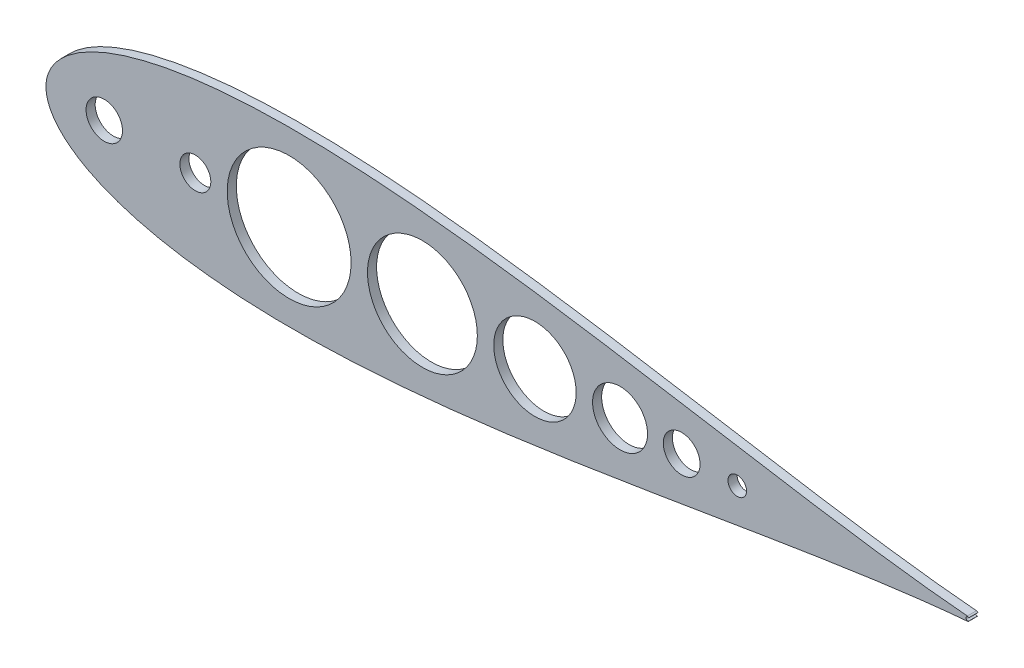
SolidWorks part; units mm, degrees
material "Balsa"
ref_plane "Front Plane" through (0, 0, 0) normal (0, 0, 1) x (1, 0, 0)
ref_plane "Top Plane" through (0, 0, 0) normal (0, 1, 0) x (1, 0, 0)
ref_plane "Right Plane" through (0, 0, 0) normal (1, 0, 0) x (0, 0, -1)
curve "Curve4"
  spline degree 3 poles (100, 0, 0) (99.8498, 0.0023, 0) (99.4759, 0.008, 0) (99.1023, 0.0238, 0) (98.8789, 0.0332, 0) knots 0 0 0 0 0.401829 1 1 1 1
curve "Curve5"
  spline degree 3 poles (99.3714, -0.0082, 0) (100.2526, 0, 0) (99.3714, 0.0082, 0) (98.8504, 0.035, 0) (97.904, 0.0811, 0) (96.8285, 0.1543, 0) (95.5159, 0.2583, 0) (94.013, 0.3972, 0) (92.313, 0.574, 0) (90.4281, 0.791, 0) (88.3655, 1.0495, 0) (86.1348, 1.3497, 0) (83.7456, 1.691, 0) (81.2082, 2.0715, 0) (78.5335, 2.4886, 0) (75.7326, 2.9386, 0) (72.8172, 3.4168, 0) (69.799, 3.9177, 0) (66.6904, 4.435, 0) (63.5039, 4.9616, 0) (60.2521, 5.4899, 0) (56.948, 6.0119, 0) (53.6049, 6.519, 0) (50.2363, 7.0024, 0) (46.8558, 7.4534, 0) (43.4774, 7.8632, 0) (40.1152, 8.2232, 0) (36.7837, 8.5249, 0) (33.4975, 8.7606, 0) (30.2716, 8.923, 0) (27.1211, 9.0055, 0) (24.0614, 9.0025, 0) (21.108, 8.909, 0) (18.277, 8.7213, 0) (15.5843, 8.4369, 0) (13.0466, 8.0543, 0) (10.6806, 7.5735, 0) (8.5039, 6.996, 0) (6.5349, 6.3253, 0) (4.7933, 5.5673, 0) (3.3001, 4.7321, 0) (2.0777, 3.8366, 0) (1.1467, 2.91, 0) (0.5165, 2.0014, 0) (0.165, 1.1816, 0) (0.0231, 0.524, 0) (-0.0093, 0, 0) (0.0231, -0.524, 0) (0.165, -1.1816, 0) (0.5165, -2.0014, 0) (1.1467, -2.91, 0) (2.0777, -3.8366, 0) (3.3001, -4.7321, 0) (4.7933, -5.5673, 0) (6.5349, -6.3253, 0) (8.5039, -6.996, 0) (10.6806, -7.5735, 0) (13.0466, -8.0543, 0) (15.5843, -8.4369, 0) (18.277, -8.7213, 0) (21.108, -8.909, 0) (24.0614, -9.0025, 0) (27.1211, -9.0055, 0) (30.2716, -8.923, 0) (33.4975, -8.7606, 0) (36.7837, -8.5249, 0) (40.1152, -8.2232, 0) (43.4774, -7.8632, 0) (46.8558, -7.4534, 0) (50.2363, -7.0024, 0) (53.6049, -6.519, 0) (56.948, -6.0119, 0) (60.2521, -5.4899, 0) (63.5039, -4.9616, 0) (66.6904, -4.435, 0) (69.799, -3.9177, 0) (72.8172, -3.4168, 0) (75.7326, -2.9386, 0) (78.5335, -2.4886, 0) (81.2082, -2.0715, 0) (83.7456, -1.691, 0) (86.1348, -1.3497, 0) (88.3655, -1.0495, 0) (90.4281, -0.791, 0) (92.313, -0.574, 0) (94.013, -0.3972, 0) (95.5159, -0.2583, 0) (96.8285, -0.1543, 0) (97.904, -0.0811, 0) (98.8504, -0.035, 0) (99.3714, -0.0082, 0) (100.2526, 0, 0) (99.3714, 0.0082, 0) knots -0.009667 -0.005395 -0.002168 0 0.002168 0.005395 0.009667 0.014967 0.021271 0.028553 0.036781 0.04592 0.055932 0.066773 0.078397 0.090755 0.103793 0.117456 0.131686 0.146422 0.1616 0.177156 0.193024 0.209135 0.225421 0.241812 0.258238 0.274629 0.290914 0.307025 0.322893 0.338448 0.353626 0.368361 0.38259 0.396253 0.40929 0.421647 0.43327 0.444109 0.454119 0.463255 0.471479 0.478755 0.485052 0.490344 0.49461 0.497833 0.5 0.502167 0.50539 0.509656 0.514948 0.521245 0.528521 0.536745 0.545881 0.555891 0.56673 0.578353 0.59071 0.603747 0.61741 0.631639 0.646374 0.661552 0.677107 0.692975 0.709086 0.725371 0.741762 0.758188 0.774579 0.790865 0.806976 0.822844 0.8384 0.853578 0.868314 0.882544 0.896207 0.909245 0.921603 0.933227 0.944068 0.95408 0.963219 0.971447 0.978729 0.985033 0.990333 0.994605 0.997832 1 1.002168 1.005395 1.009667 periodic
sketch "Sketch2" plane through (0, 0, 0) normal (0, 0, 1) x (1, 0, 0)
  line L0 (100, 0) -> (0, 0) construction
  line L2 (93.345, 0) -> (114.935, 0) construction
  line L4 (643.5991, 0) -> (643.5991, -1.016)
  line L9 (0, 0) -> (643.9668, 0)
  line L13 (460.661, 0) -> (473.361, 0)
  circle A0 centre (104.14, 0) radius 10.795 construction
  arc A2 (641.5671, 0) -> (644.1071, 0) centre (642.8371, 0) ccw
  circle A4 centre (104.14, 0) radius 10.795
  circle A9 centre (40.64, 0) radius 12.7
  circle A14 centre (642.3793, 0) radius 1.5875 construction
  arc A15 (642.5108, -1.582) -> (642.5108, 1.582) centre (642.3793, 0) ccw
  spline S2 degree 3 poles (666.3448, -0.0547) (672.2538, 0) (666.3448, 0.0547) (662.8509, 0.2344) (656.505, 0.5436) (649.293, 1.0348) (640.4916, 1.7319) (630.4138, 2.6634) (619.0141, 3.8493) (606.375, 5.3044) (592.5439, 7.0376) (577.5855, 9.0506) (561.5643, 11.3389) (544.5497, 13.8907) (526.6141, 16.6877) (507.8326, 19.7051) (488.2827, 22.9117) (468.0444, 26.2704) (447.1994, 29.739) (425.8316, 33.2703) (404.0263, 36.8132) (381.8707, 40.3133) (359.4533, 43.7135) (336.8645, 46.9554) (314.1962, 49.9798) (291.5418, 52.7277) (268.9963, 55.1412) (246.6566, 57.1646) (224.6209, 58.7452) (202.9892, 59.8341) (181.8631, 60.3875) (161.3458, 60.367) (141.542, 59.7399) (122.5581, 58.4818) (104.5023, 56.5743) (87.485, 54.0089) (71.6197, 50.7848) (57.0237, 46.9125) (43.8205, 42.415) (32.1416, 37.3322) (22.1291, 31.7315) (13.9324, 25.7264) (7.6896, 19.5132) (3.4631, 13.4204) (1.1063, 7.9234) (0.1546, 3.5138) (-0.0622, 0) (0.1546, -3.5138) (1.1063, -7.9234) (3.4631, -13.4204) (7.6896, -19.5132) (13.9324, -25.7264) (22.1291, -31.7315) (32.1416, -37.3322) (43.8205, -42.415) (57.0237, -46.9125) (71.6197, -50.7848) (87.485, -54.0089) (104.5023, -56.5743) (122.5581, -58.4818) (141.542, -59.7399) (161.3458, -60.367) (181.8631, -60.3875) (202.9892, -59.8341) (224.6209, -58.7452) (246.6566, -57.1646) (268.9963, -55.1412) (291.5418, -52.7277) (314.1962, -49.9798) (336.8645, -46.9554) (359.4533, -43.7135) (381.8707, -40.3133) (404.0263, -36.8132) (425.8316, -33.2703) (447.1994, -29.739) (468.0444, -26.2704) (488.2827, -22.9117) (507.8326, -19.7051) (526.6141, -16.6877) (544.5497, -13.8907) (561.5643, -11.3389) (577.5855, -9.0506) (592.5439, -7.0376) (606.375, -5.3044) (619.0141, -3.8493) (630.4138, -2.6634) (640.4916, -1.7319) (649.293, -1.0348) (656.505, -0.5436) (662.8509, -0.2344) (666.3448, -0.0547) (672.2538, 0) (666.3448, 0.0547) knots -0.009667 -0.005395 -0.002168 0 0.002168 0.005395 0.009667 0.014967 0.021271 0.028553 0.036781 0.04592 0.055932 0.066773 0.078397 0.090755 0.103793 0.117456 0.131686 0.146422 0.1616 0.177156 0.193024 0.209135 0.225421 0.241812 0.258238 0.274629 0.290914 0.307025 0.322893 0.338448 0.353626 0.368361 0.38259 0.396253 0.40929 0.421647 0.43327 0.444109 0.454119 0.463255 0.471479 0.478755 0.485052 0.490344 0.49461 0.497833 0.5 0.502167 0.50539 0.509656 0.514948 0.521245 0.528521 0.536745 0.545881 0.555891 0.56673 0.578353 0.59071 0.603747 0.61741 0.631639 0.646374 0.661552 0.677107 0.692975 0.709086 0.725371 0.741762 0.758188 0.774579 0.790865 0.806976 0.822844 0.8384 0.853578 0.868314 0.882544 0.896207 0.909245 0.921603 0.933227 0.944068 0.95408 0.963219 0.971447 0.978729 0.985033 0.990333 0.994605 0.997832 1 1.002168 1.005395 1.009667 only from (670.56, 0) to (670.56, 0)
  point P2 (167.64, 0)
  dimension "D2" = 21.59
  dimension "D8" = 25.4
  dimension "D10" = 3.175
  dimension "D1" = 167.64
  dimension "D6" = 63.5
  dimension "D9" = 63.5
  dimension "D3" = 1.016
  dimension "D4" = 1.27
extrude "Boss-Extrude1" add sketch "Sketch2" along normal blind 6.35
sketch "Sketch3" plane through (0, 0, 6.35) normal (0, 0, 1) x (1, 0, 0)
  line L0 (84.14, -12.7) -> (62.637, -12.7) construction
  line L1 (430.4749, -1041.2705) -> (430.4749, 48958.7295) construction
  line L2 (114.935, 0) -> (641.5671, 0) construction
  line L3 (27.94, 0) -> (0, 0)
  line L4 (641.5671, 0) -> (114.935, 0)
  line L5 (93.345, 0) -> (53.34, 0)
  line L6 (27.94, 0) -> (0, 0)
  line L7 (212.768, -1000) -> (212.768, 49000) construction
  line L8 (93.345, 0) -> (53.34, 0)
  line L9 (224.198, -1000) -> (224.198, 49000) construction
  line L10 (300.8092, -1000) -> (300.8092, 49000) construction
  line L11 (312.2392, -1000) -> (312.2392, 49000) construction
  line L12 (369.7207, -1000) -> (369.7207, 49000) construction
  line L13 (93.345, -17.145) -> (65.0689, -17.145) construction
  line L14 (419.5047, -1000) -> (419.5047, 49000) construction
  line L15 (126.365, -1000) -> (126.365, 49000) construction
  line L16 (381.1507, -1000) -> (381.1507, 49000) construction
  line L17 (52.7726, -27.2676) -> (52.7726, -27.2676) construction
  arc A0 (36.4352, -25.0495) -> (62.637, -12.7) centre (40.64, 0) ccw construction
  circle A2 centre (169.5665, 0) radius 43.2015
  arc A3 (642.5108, -1.582) -> (643.5991, -1.016) centre (642.3793, 0) ccw
  arc A4 (93.345, 0) -> (114.935, 0) centre (104.14, 0) ccw
  arc A5 (27.94, 0) -> (53.34, 0) centre (40.64, 0) ccw
  arc A6 (642.5108, -1.582) -> (643.5991, -1.016) centre (642.3793, 0) ccw
  circle A7 centre (262.5036, 0) radius 38.3056
  arc A8 (27.94, 0) -> (53.34, 0) centre (40.64, 0) ccw
  circle A9 centre (340.9799, 0) radius 28.7408
  circle A10 centre (400.3277, 0) radius 19.177
  circle A11 centre (443.3019, 0) radius 12.827
  circle A12 centre (482.0825, 0) radius 6.477
  arc A13 (52.7726, -27.2676) -> (65.0689, -17.145) centre (40.64, 0) ccw construction
  arc A14 (638.2053, 15.2585) -> (638.2053, 15.2585) centre (638.2053, 15.2585) ccw construction
  arc A18 (641.5671, 0) -> (643.5991, -1.016) centre (642.8371, 0) ccw
  arc A19 (641.5671, 0) -> (643.5991, -1.016) centre (642.8371, 0) ccw
  spline S1 degree 3 poles (1488.1541, -2580.0534) (314.1987, 184.2642) (-15.4092, 68.5977) (1.1063, -7.9234) (3.4631, -13.4204) (7.6896, -19.5132) (13.9324, -25.7264) (22.1291, -31.7315) (32.1416, -37.3322) (43.8205, -42.415) (57.0237, -46.9125) (71.6197, -50.7848) (87.485, -54.0089) (104.5023, -56.5743) (122.5581, -58.4818) (141.542, -59.7399) (161.3458, -60.367) (181.8631, -60.3875) (202.9892, -59.8341) (224.6209, -58.7452) (246.6566, -57.1646) (268.9963, -55.1412) (291.5418, -52.7277) (314.1962, -49.9798) (336.8645, -46.9554) (359.4533, -43.7135) (381.8707, -40.3133) (404.0263, -36.8132) (425.8316, -33.2703) (447.1994, -29.739) (468.0444, -26.2704) (488.2827, -22.9117) (507.8326, -19.7051) (526.6141, -16.6877) (544.5497, -13.8907) (561.5643, -11.3389) (577.5855, -9.0506) (592.5439, -7.0376) (606.375, -5.3044) (619.0141, -3.8493) (630.4138, -2.6634) (754.7119, 8.8252) (895.5191, -9.0089) (-2343.84, -283.812) knots 0.342093 0.342093 0.342093 0.342093 0.502167 0.50539 0.509656 0.514948 0.521245 0.528521 0.536745 0.545881 0.555891 0.56673 0.578353 0.59071 0.603747 0.61741 0.631639 0.646374 0.661552 0.677107 0.692975 0.709086 0.725371 0.741762 0.758188 0.774579 0.790865 0.806976 0.822844 0.8384 0.853578 0.868314 0.882544 0.896207 0.909245 0.921603 0.933227 0.944068 0.95408 0.963219 0.971447 0.978729 1.23227 1.23227 1.23227 1.23227 only from (0, 0) to (642.5108, -1.582)
  spline S2 degree 3 poles (0, 0) (0, -1.0075) (0.1546, -3.5138) (1.1063, -7.9234) (3.4631, -13.4204) (7.6896, -19.5132) (13.9324, -25.7264) (22.1291, -31.7315) (32.1416, -37.3322) (43.8205, -42.415) (57.0237, -46.9125) (71.6197, -50.7848) (87.485, -54.0089) (104.5023, -56.5743) (122.5581, -58.4818) (141.542, -59.7399) (161.3458, -60.367) (181.8631, -60.3875) (202.9892, -59.8341) (224.6209, -58.7452) (246.6566, -57.1646) (268.9963, -55.1412) (291.5418, -52.7277) (314.1962, -49.9798) (336.8645, -46.9554) (359.4533, -43.7135) (381.8707, -40.3133) (404.0263, -36.8132) (425.8316, -33.2703) (447.1994, -29.739) (468.0444, -26.2704) (488.2827, -22.9117) (507.8326, -19.7051) (526.6141, -16.6877) (544.5497, -13.8907) (561.5643, -11.3389) (577.5855, -9.0506) (592.5439, -7.0376) (606.375, -5.3044) (619.0141, -3.8493) (630.4138, -2.6634) (638.0937, -1.9535) (641.9934, -1.6251) (642.5108, -1.582) knots 0.5 0.5 0.5 0.5 0.502167 0.50539 0.509656 0.514948 0.521245 0.528521 0.536745 0.545881 0.555891 0.56673 0.578353 0.59071 0.603747 0.61741 0.631639 0.646374 0.661552 0.677107 0.692975 0.709086 0.725371 0.741762 0.758188 0.774579 0.790865 0.806976 0.822844 0.8384 0.853578 0.868314 0.882544 0.896207 0.909245 0.921603 0.933227 0.944068 0.95408 0.963219 0.971447 0.978729 0.979843 0.979843 0.979843 0.979843
  spline S4 degree 1 poles (52.7726, -27.2676) (638.2053, 15.2585) knots 0 0 1 1 construction
  spline S5 degree 3 poles (52.7726, -27.2676) (54.098, -27.7509) (56.7529, -28.6784) (62.1794, -30.4243) (69.1006, -32.3953) (77.5892, -34.4571) (89.0862, -36.8389) (103.7331, -39.1926) (125.3657, -41.6037) (144.2709, -42.7116) (163.2853, -43.1964) (177.6693, -43.2555) (201.2447, -42.8023) (227.4371, -41.4675) (254.4928, -39.2877) (277.8401, -36.9937) (301.0423, -34.3583) (330.3789, -30.5811) (368.329, -25.1309) (404.83, -19.3409) (435.2358, -14.3425) (451.6826, -11.6119) (464.2574, -9.5208) (476.8398, -7.4307) (497.3171, -4.0443) (526.9629, 0.7645) (562.929, 6.2684) (594.1055, 10.5252) (616.0859, 13.0867) (628.694, 14.3901) (635.0364, 14.9826) (638.2053, 15.2585) knots 0.548481 0.548481 0.548481 0.548481 0.551835 0.555189 0.561898 0.568606 0.575315 0.588731 0.602148 0.62409 0.630798 0.644215 0.655815 0.682649 0.701659 0.715076 0.733763 0.752449 0.779283 0.816817 0.832298 0.845715 0.852722 0.859728 0.873145 0.897318 0.924152 0.950985 0.964402 0.971111 0.977819 0.977819 0.977819 0.977819 construction
  line M19 (641.5671, 0) -> (114.935, 0)
  dimension "D3" = 11.43
  dimension "D7" = 38.354
  dimension "D8" = 25.654
  dimension "D9" = 12.954
  dimension "D4" = 11.43
  dimension "D5" = 11.43
  dimension "D6" = 11.43
  dimension "D1" = 0
  dimension "D10" = 17.145
extrude "Cut-Extrude2" cut sketch "Sketch3" against normal through all both and the other way through all contours A2 M19 | A7 M19 | A9 M19 | A10 M19 | A11 M19 | A12 M19
mirror "Mirror1" about plane through (0, 0, 0) normal (0, 1, 0) of "Cut-Extrude2", "Boss-Extrude1"
equation "\"0.5n\"=0"
equation "\"ROD DIAM\"= \"D2@Sketch2\""
